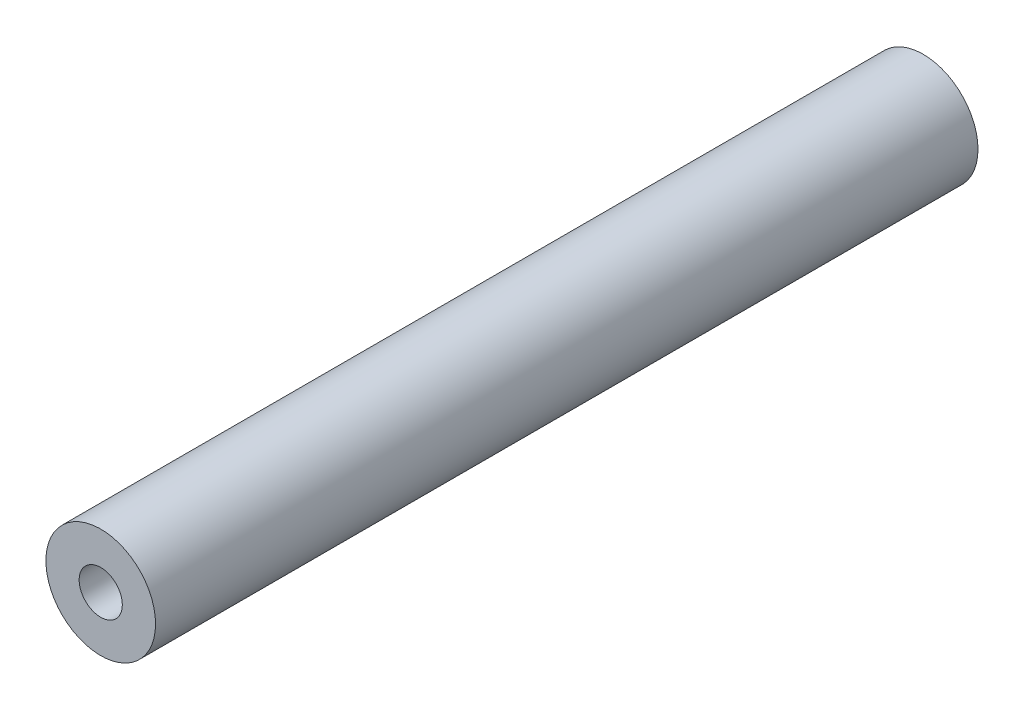
SolidWorks part; units mm, degrees
material "Default"
ref_plane "Top" through (0, 0, 0) normal (0, 0, 1) x (1, 0, 0)
ref_plane "Right" through (0, 0, 0) normal (0, 1, 0) x (1, 0, 0)
ref_plane "Front" through (0, 0, 0) normal (1, 0, 0) x (0, 0, -1)
sketch "Sketch1" plane through (0, 0, 48.35) normal (0, 0, 1) x (1, 0, 0)
  circle A1 centre (53.781, -135.4499) radius 2.54
  circle A2 centre (53.781, -135.4499) radius 1
  circle A3 centre (53.781, -135.4499) radius 1 construction
  dimension "D1" = 2
  dimension "D2" = 5.08
extrude "Boss-Extrude1" add sketch "Sketch1" against normal blind 38.1
